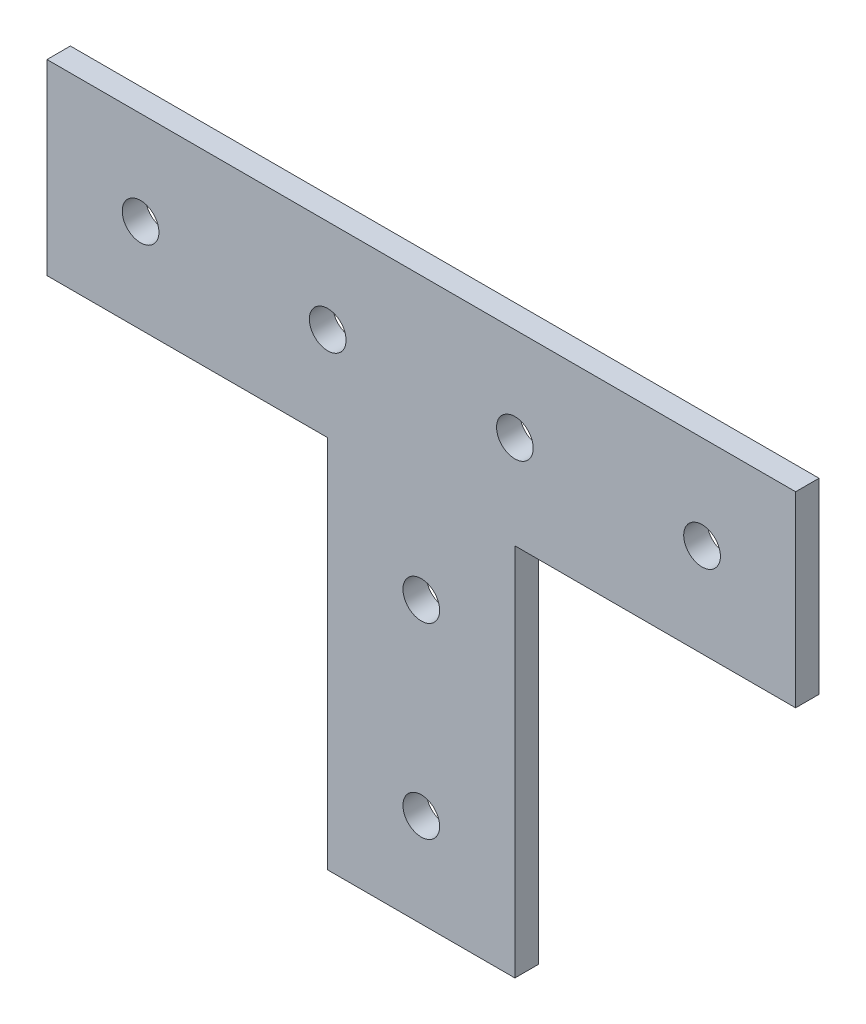
SolidWorks part; units mm, degrees
ref_plane "Front" through (0, 0, 0) normal (0, 0, 1) x (1, 0, 0)
ref_plane "Top" through (0, 0, 0) normal (0, 1, 0) x (1, 0, 0)
ref_plane "Right" through (0, 0, 0) normal (1, 0, 0) x (0, 0, -1)
sketch "Sketch1" plane through (0, 0, 0) normal (0, 0, 1) x (1, 0, 0)
  line L0 (-50.8, 25.4) -> (50.8, 25.4)
  line L1 (-12.7, -25.4) -> (12.7, -25.4)
  line L2 (-12.7, -25.4) -> (-12.7, 25.4)
  line L4 (12.7, -25.4) -> (12.7, 25.4)
  line L5 (-12.7, -25.4) -> (12.7, 25.4) construction
  line L6 (-12.7, 25.4) -> (12.7, -25.4) construction
  line L7 (50.8, 25.4) -> (50.8, 50.8)
  line L8 (50.8, 50.8) -> (-50.8, 50.8)
  line L9 (-50.8, 50.8) -> (-50.8, 25.4)
  line L10 (-12.7, 25.4) -> (12.7, 25.4) construction
  line L11 (-50.8, 38.1) -> (50.8, 38.1) construction
  line L12 (0, 25.4) -> (0, -25.4) construction
  circle A0 centre (0, 12.7) radius 2.4892
  circle A1 centre (0, -12.7) radius 2.4892
  circle A2 centre (12.7, 38.1) radius 2.4892
  circle A3 centre (-12.7, 38.1) radius 2.4892
  circle A4 centre (-38.1, 38.1) radius 2.4892
  circle A5 centre (38.1, 38.1) radius 2.4892
  point P0 (0, 0)
  point P6 (0, 25.4)
  dimension "D5" = 25.4
  dimension "D9" = 4.9784
  dimension "D10" = 12.7
  dimension "D1" = 25.4
  dimension "D2" = 50.8
  dimension "D3" = 101.6
  dimension "D4" = 25.4
  dimension "D6" = 25.4
  dimension "D7" = 12.7
  dimension "D8" = 25.4
  dimension "D11" = 25.4
extrude "Boss-Extrude1" add sketch "Sketch1" along normal blind 3.175 contours L8 L9 L0 L7 A4 A3 A2 | L1 L4 L0 L2 A1 A0
